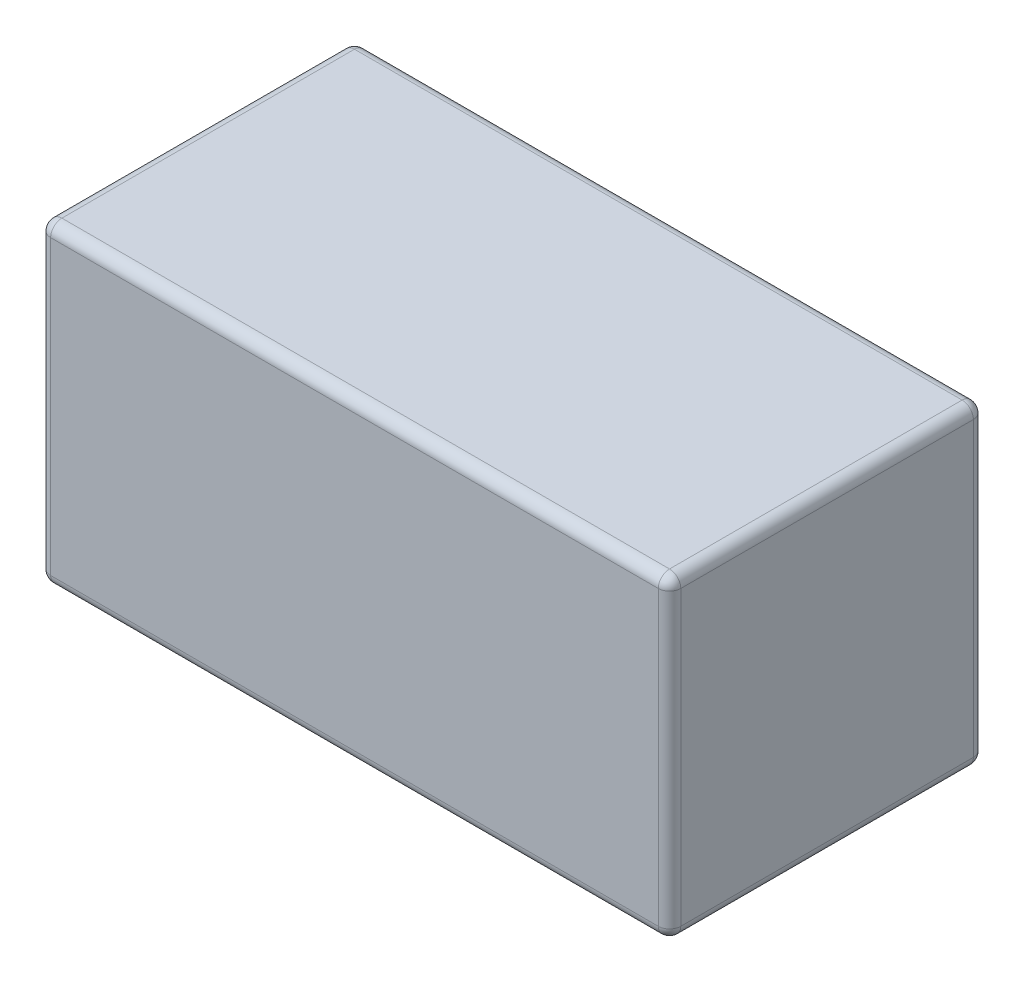
SolidWorks part; units mm, degrees
ref_plane "Front Plane" through (0, 0, 0) normal (0, 0, 1) x (1, 0, 0)
ref_plane "Top Plane" through (0, 0, 0) normal (0, 1, 0) x (1, 0, 0)
ref_plane "Right Plane" through (0, 0, 0) normal (1, 0, 0) x (0, 0, -1)
sketch "Sketch1" plane through (0, 0, 0) normal (0, 1, 0) x (1, 0, 0)
  line L1 (0, 0) -> (71.12, 0)
  line L2 (0, 0) -> (0, 35.56)
  line L3 (0, 35.56) -> (71.12, 35.56)
  line L4 (71.12, 0) -> (71.12, 35.56)
  dimension "D1" = 35.56
  dimension "D2" = 71.12
extrude "Boss-Extrude1" add sketch "Sketch1" along normal blind 35.56
fillet "Fillet1" radius 1.27 12 edges at (0, 0, -17.78) (35.56, 0, -35.56) (0, 17.78, -35.56) (71.12, 17.78, -35.56) (71.12, 0, -17.78) (35.56, 0, 0) (0, 17.78, 0) (0, 35.56, -17.78) (35.56, 35.56, -35.56) (71.12, 17.78, 0) (71.12, 35.56, -17.78) (35.56, 35.56, 0)
